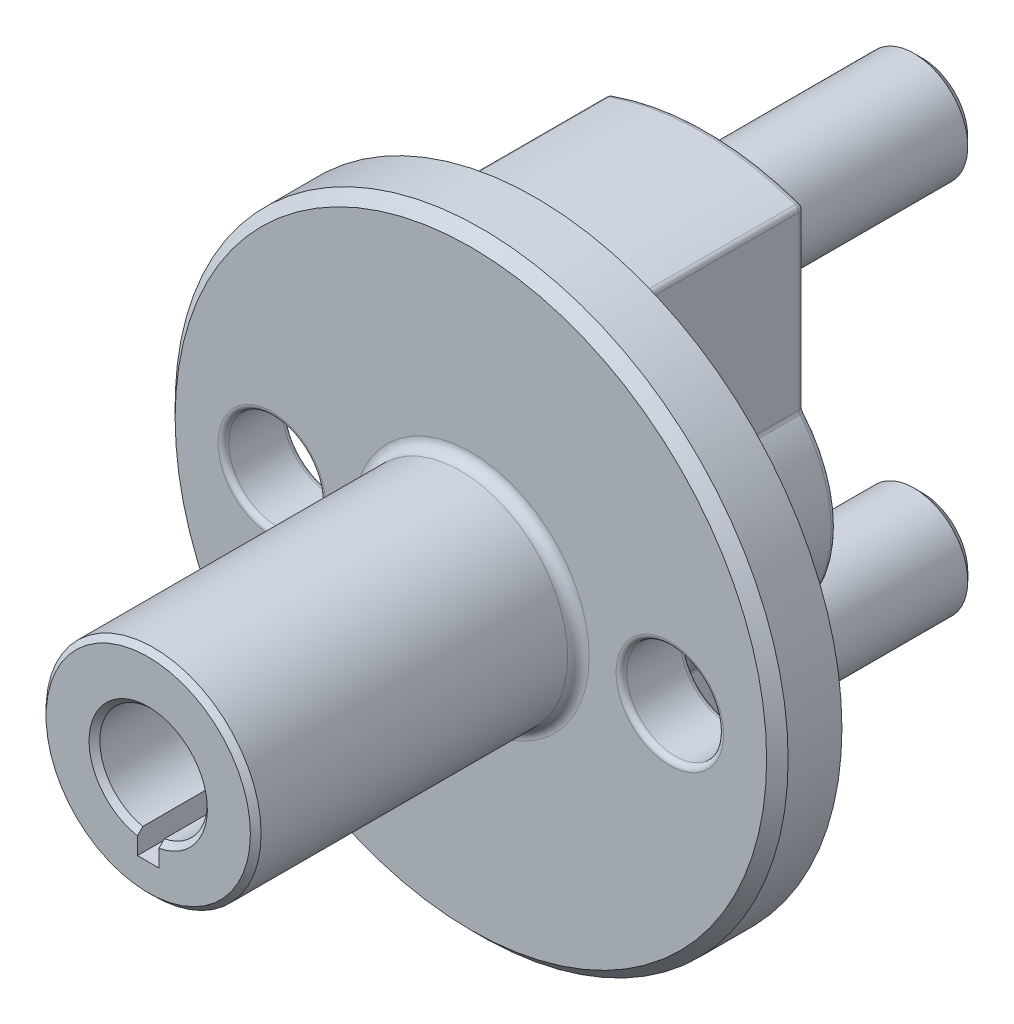
SolidWorks part; units mm, degrees
material "PVC Rigid"
ref_plane "Front Plane" through (0, 0, 0) normal (0, 0, 1) x (1, 0, 0)
ref_plane "Top Plane" through (0, 0, 0) normal (0, 1, 0) x (1, 0, 0)
ref_plane "Right Plane" through (0, 0, 0) normal (1, 0, 0) x (0, 0, -1)
sketch "Sketch1" plane through (0, 0, 0) normal (0, 0, 1) x (1, 0, 0)
  circle A0 centre (0, 0) radius 28.5
  dimension "D1" = 57
extrude "Boss-Extrude1" add sketch "Sketch1" along normal blind 6
ref_plane "Plane1" through (0, 0, 0) normal (0, 0, -1) x (-1, 0, 0)
sketch "Sketch3" plane through (0, 0, 0) normal (0, 0, -1) x (-1, 0, 0)
  line L0 (0, 28.5) -> (0, -28.5) construction
  line L1 (-9, 24.3926) -> (-9, 7.9373)
  line L2 (9, 24.3926) -> (9, 7.9373)
  line L3 (-9, -7.9373) -> (-9, -24.3926)
  line L4 (9, -7.9373) -> (9, -24.3926)
  arc A0 (-9, -24.3926) -> (9, -24.3926) centre (0, 0) ccw
  circle A1 centre (0, 0) radius 28.5 construction
  arc A2 (9, 24.3926) -> (-9, 24.3926) centre (0, 0) ccw
  arc A3 (-9, 7.9373) -> (-9, -7.9373) centre (0, 0) ccw
  arc A4 (9, -7.9373) -> (9, 7.9373) centre (0, 0) ccw
  dimension "D1" = 52
  dimension "D3" = 24
  dimension "D2" = 9
extrude "Boss-Extrude2" add sketch "Sketch3" along normal blind 16
chamfer "Chamfer1" distance 1 angle 45 1 edges at (28.5, 0, 6)
fillet "Fillet1" radius 0.5 24 edges at (9, 16.1649, 0) (0, -26, 0) (-9, -24.3926, -8) (-9, -16.1649, 0) (-9, -7.9373, -8) (-12, 0, 0) (-9, 7.9373, -8) (-9, 16.1649, 0) (-9, 16.1649, -16) (-12, 0, -16) (-9, -16.1649, -16) (0, -26, -16) (9, 16.1649, -16) (9, -16.1649, -16) (9, -24.3926, -8) (9, -16.1649, 0) (9, 7.9373, -8) (12, 0, -16) (9, -7.9373, -8) (12, 0, 0) (-9, 24.3926, -8) (0, 26, -16) (9, 24.3926, -8) (0, 26, 0)
ref_plane "Plane2" through (0, 0, 6) normal (0, 0, 1) x (1, 0, 0)
sketch "Sketch4" plane through (0, 0, 6) normal (0, 0, 1) x (1, 0, 0)
  line L0 (-28.5, 0) -> (28.5, 0) construction
  line L1 (0, 28.5) -> (0, -28.5) construction
  circle A0 centre (0, 0) radius 28.5 construction
  circle A1 centre (18.5, 0) radius 4.5
  circle A2 centre (-18.5, 0) radius 4.5
  dimension "D1" = 9
  dimension "D2" = 9
  dimension "D3" = 37
  dimension "D4" = 18.5
extrude "Cut-Extrude1" cut sketch "Sketch4" against normal through all
fillet "Fillet2" radius 0.5 4 edges at (23, 0, 0) (23, 0, 6) (-14, 0, 0) (-14, 0, 6)
sketch "Sketch5" plane through (0, 0, 6) normal (0, 0, 1) x (1, 0, 0)
  circle A0 centre (0, 0) radius 10
  dimension "D1" = 20
extrude "Boss-Extrude3" add sketch "Sketch5" along normal blind 30
fillet "Fillet3" radius 1 1 edges at (10, 0, 6)
chamfer "Chamfer2" distance 0.5 angle 45 1 edges at (10, 0, 36)
ref_plane "Plane3" through (0, 0, -16) normal (0, 0, -1) x (-1, 0, 0)
sketch "Sketch6" plane through (0, 0, -16) normal (0, 0, -1) x (-1, 0, 0)
  line L0 (0, 28.5) -> (0, -28.5) construction
  line L1 (-28.5, 0) -> (28.5, 0) construction
  circle A0 centre (0, 0) radius 28.5 construction
  circle A1 centre (0, 17.5) radius 5
  circle A2 centre (0, -17.5) radius 5
  dimension "D1" = 10
  dimension "D2" = 35
extrude "Boss-Extrude4" add sketch "Sketch6" along normal blind 20
chamfer "Chamfer3" distance 0.8 angle 45 2 edges at (5, -17.5, -36) (-5, 17.5, -36)
ref_plane "Plane4" through (0, 0, 36) normal (0, 0, 1) x (1, 0, 0)
sketch "Sketch7" plane through (0, 0, 36) normal (0, 0, 1) x (1, 0, 0)
  line L0 (0, 5) -> (0, -5) construction
  line L1 (-1, -4.899) -> (-1, -7)
  line L2 (-1, -7) -> (1, -7)
  line L3 (1, -7) -> (1, -4.899)
  arc A0 (1, -4.899) -> (-1, -4.899) centre (0, 0) ccw
  dimension "D1" = 10
  dimension "D2" = 2
  dimension "D3" = 2
  dimension "D4" = 1
extrude "Cut-Extrude2" cut sketch "Sketch7" against normal blind 30
chamfer "Chamfer4" distance 0.5 angle 45 1 edges at (0, 5, 36)
